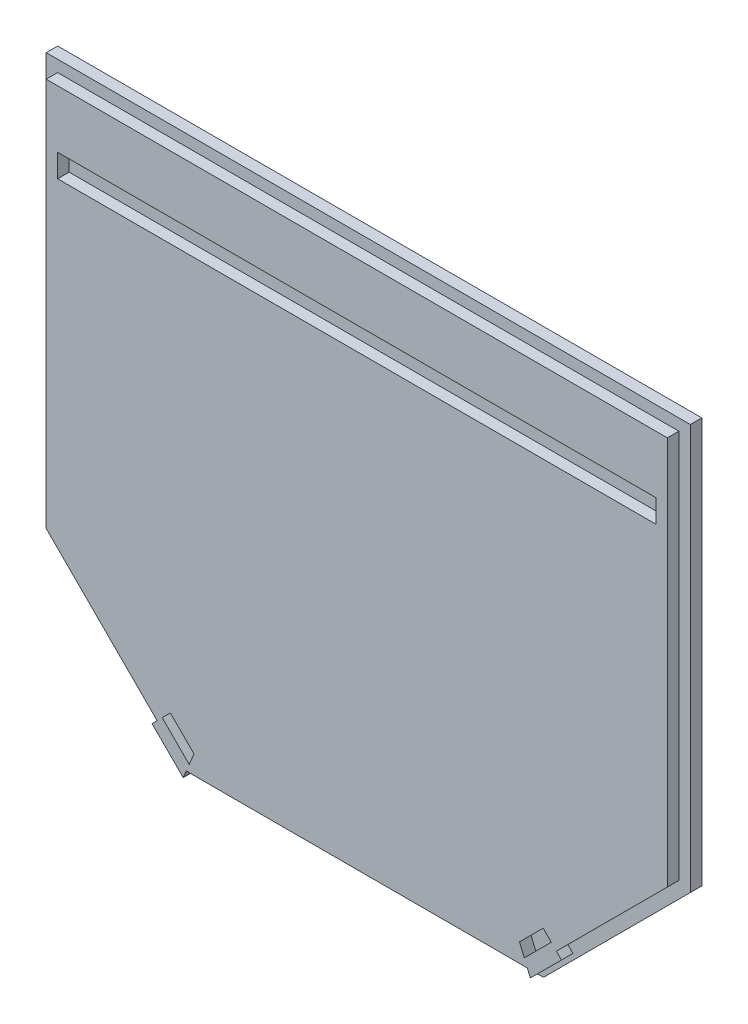
SolidWorks part; units mm, degrees
ref_plane "Front Plane" through (0, 0, 0) normal (0, 0, 1) x (1, 0, 0)
ref_plane "Top Plane" through (0, 0, 0) normal (0, 1, 0) x (1, 0, 0)
ref_plane "Right Plane" through (0, 0, 0) normal (1, 0, 0) x (0, 0, -1)
sketch "Sketch1" plane through (0, 0, 0) normal (0, 0, 1) x (1, 0, 0)
  line L0 (0, 0) -> (355.6, 0)
  line L1 (0, 0) -> (0, -223.774)
  line L2 (81.026, -304.8) -> (274.574, -304.8)
  line L3 (355.6, -223.774) -> (355.6, 0)
  line L4 (81.026, -304.8) -> (63.0655, -286.8395)
  line L5 (63.0655, -286.8395) -> (0, -223.774)
  line L6 (177.8, -304.8) -> (177.8, 0) construction
  line L7 (292.5345, -286.8395) -> (355.6, -223.774)
  line L8 (274.574, -304.8) -> (292.5345, -286.8395)
  dimension "D1" = 355.6
  dimension "D2" = 193.548
  dimension "D4" = 25.4
  dimension "D5" = 45
  dimension "D9" = 304.8
extrude "Boss-Extrude1" add sketch "Sketch1" along normal blind 12.7
sketch "Sketch2" plane through (0, 0, 12.7) normal (0, 0, 1) x (1, 0, 0)
  line L0 (6.35, -221.1437) -> (67.6075, -282.4012)
  line L1 (83.6563, -298.45) -> (271.9437, -298.45)
  line L2 (287.9925, -282.4012) -> (349.25, -221.1437)
  line L3 (349.25, -221.1437) -> (349.25, -6.35)
  line L4 (349.25, -6.35) -> (6.35, -6.35)
  line L5 (6.35, -6.35) -> (6.35, -221.1437)
  line L6 (0, -223.774) -> (81.026, -304.8) construction
  line L7 (81.026, -304.8) -> (274.574, -304.8) construction
  line L8 (274.574, -304.8) -> (355.6, -223.774) construction
  line L9 (355.6, -223.774) -> (355.6, 0) construction
  line L10 (0, 0) -> (0, -223.774) construction
  line L11 (355.6, 0) -> (0, 0) construction
  line L21 (81.026, -304.8) -> (83.6563, -298.45) construction
  line L23 (73.3233, -276.6854) -> (73.0994, -276.9093) construction
  line L24 (64.7877, -285.221) -> (82.0045, -302.4378)
  line L25 (82.0045, -302.4378) -> (83.6563, -298.45)
  line L26 (64.7877, -285.221) -> (67.6075, -282.4012)
  line L27 (0, 0) -> (0, -223.774)
  line L28 (0, -223.774) -> (81.026, -304.8)
  line L29 (81.026, -304.8) -> (274.574, -304.8)
  line L30 (274.574, -304.8) -> (355.6, -223.774)
  line L31 (355.6, -223.774) -> (355.6, 0)
  line L32 (355.6, 0) -> (0, 0)
  line L33 (177.8, -298.45) -> (177.8, 0) construction
  line L34 (12.7, -38.1) -> (342.9, -38.1)
  line L35 (12.7, -38.1) -> (12.7, -50.8)
  line L36 (12.7, -50.8) -> (342.9, -50.8)
  line L37 (342.9, -38.1) -> (342.9, -50.8)
  line L38 (273.5955, -302.4378) -> (271.9437, -298.45)
  line L39 (290.8123, -285.221) -> (273.5955, -302.4378)
  line L40 (290.8123, -285.221) -> (287.9925, -282.4012)
  line L41 (271.9437, -298.45) -> (349.25, -221.1437) construction
  line L42 (6.35, -221.1437) -> (83.6563, -298.45) construction
  line M13 (0, 0) -> (0, -223.774)
  line M14 (0, -223.774) -> (81.026, -304.8)
  line M15 (81.026, -304.8) -> (274.574, -304.8)
  line M16 (274.574, -304.8) -> (355.6, -223.774)
  line M17 (355.6, -223.774) -> (355.6, 0)
  line M18 (355.6, 0) -> (0, 0)
  dimension "D2" = 6.35
  dimension "D3" = 6.35
  dimension "D4" = 6.35
  dimension "D5" = 6.35
  dimension "D6" = 6.35
  dimension "D7" = 6.35
  dimension "D8" = 6.35
  dimension "D9" = 50.8
  dimension "D10" = 12.7
  dimension "D11" = 2.3622
extrude "Cut-Extrude1" cut sketch "Sketch2" against normal blind 6.35 contours L37 L34 L35 L36 | L5 L4 L3 L2 L1 L0 M18 M13 M14 M15 M16 M17
sketch "Sketch3" plane through (0, 0, 12.7) normal (0, 0, 1) x (1, 0, 0)
  line L0 (177.8, -304.8) -> (177.8, 0) construction
  line L1 (81.026, -304.8) -> (274.574, -304.8) construction
  line L2 (355.6, 0) -> (0, 0) construction
  line L3 (81.026, -304.8) -> (83.6563, -298.45) construction
  line L4 (85.3081, -294.4622) -> (70.4008, -279.555)
  line L5 (85.3081, -294.4622) -> (87.9383, -288.1122)
  line L8 (70.4008, -279.555) -> (74.891, -275.0648)
  line L9 (74.891, -275.0648) -> (87.9383, -288.1122)
  line L10 (285.1992, -279.555) -> (280.709, -275.0648)
  line L11 (270.2919, -294.4622) -> (285.1992, -279.555)
  line L12 (270.2919, -294.4622) -> (267.6617, -288.1122)
  line L13 (280.709, -275.0648) -> (267.6617, -288.1122)
  line L14 (11.7799, -215.7138) -> (6.35, -221.1437) construction
  line L15 (6.35, -221.1437) -> (67.6075, -282.4012) construction
  dimension "D1" = 21.082
  dimension "D2" = 3.9878
  dimension "D3" = 6.35
  dimension "D4" = 90
  dimension "D5" = 67.5
extrude "Cut-Extrude3" cut sketch "Sketch3" against normal blind 6.35
